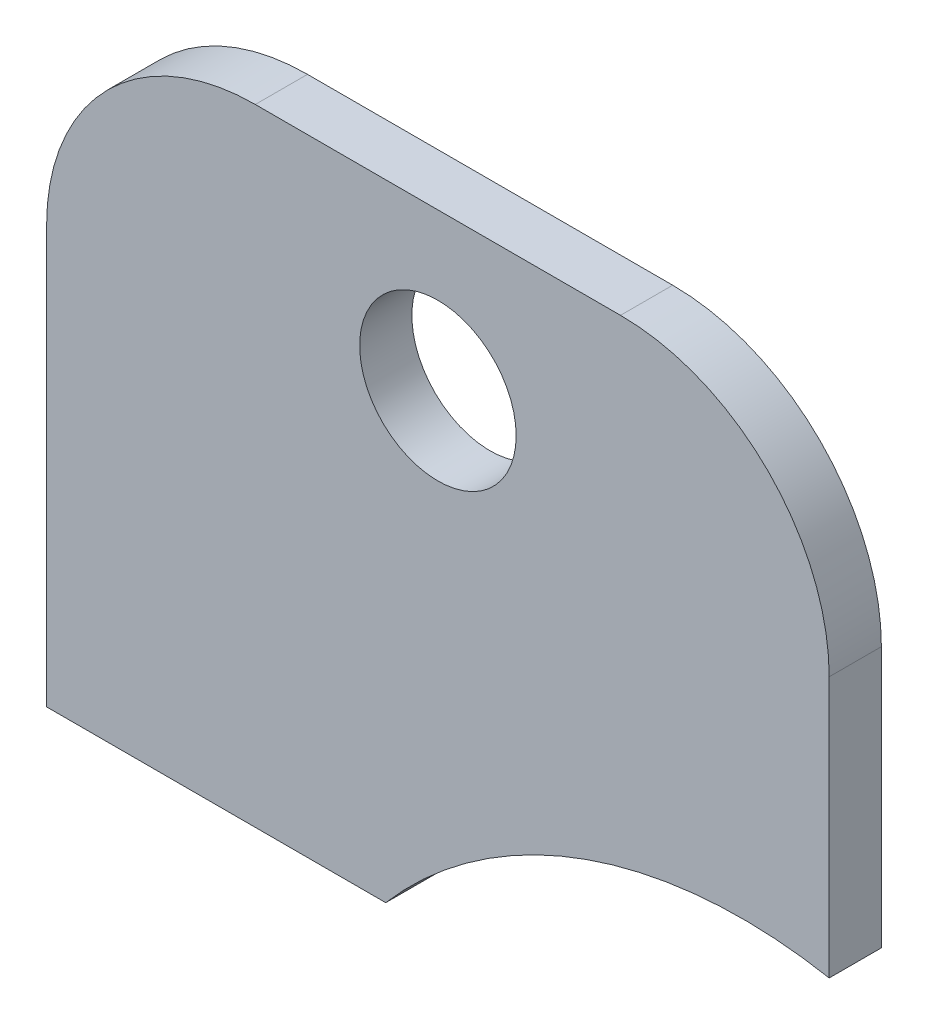
SolidWorks part; units mm, degrees
material "Stal węglowa"
ref_plane "Płaszczyzna XY" through (0, 0, 0) normal (0, 0, 1) x (1, 0, 0)
ref_plane "Płaszczyzna XZ" through (0, 0, 0) normal (0, 1, 0) x (1, 0, 0)
ref_plane "Płaszczyzna YZ" through (0, 0, 0) normal (1, 0, 0) x (0, 0, -1)
sketch "Szkic3" plane through (0, 0, 0) normal (0, 0, 1) x (1, 0, 0)
  line L1 (1470.7179, -27.5) -> (1500.7179, -27.5)
  line L2 (1500.7179, -27.5) -> (1500.7179, -45.5)
  line L6 (1470.7179, -51.5) -> (1483.7179, -51.5)
  line L7 (1470.7179, -27.5) -> (1470.7179, -51.5)
  arc A0 (1483.7179, -51.5) -> (1500.7179, -45.5) centre (1497.4033, -63.1922) cw
  dimension "D4" = 18
  dimension "D1" = 18
  dimension "D2" = 24
  dimension "D3" = 13
extrude "Dodanie-wyciągnięcie2" add sketch "Szkic3" along normal blind 2
sketch "Szkic4" plane through (0, 0, 2) normal (0, 0, 1) x (1, 0, 0)
  line L0 (1470.7179, -27.5) -> (1470.7179, -51.5) construction
  line L1 (1500.7179, -27.5) -> (1470.7179, -27.5) construction
  circle A0 centre (1485.7179, -33.5) radius 3
  dimension "D1" = 15
  dimension "D3" = 6
  dimension "D2" = 6
extrude "Wytnij-wyciągnięcie2" cut sketch "Szkic4" against normal blind 2
fillet "Zaokrąglenie1" radius 8 1 edges at (1470.7179, -27.5, 1)
fillet "Zaokrąglenie2" radius 8 1 edges at (1500.7179, -27.5, 1)
